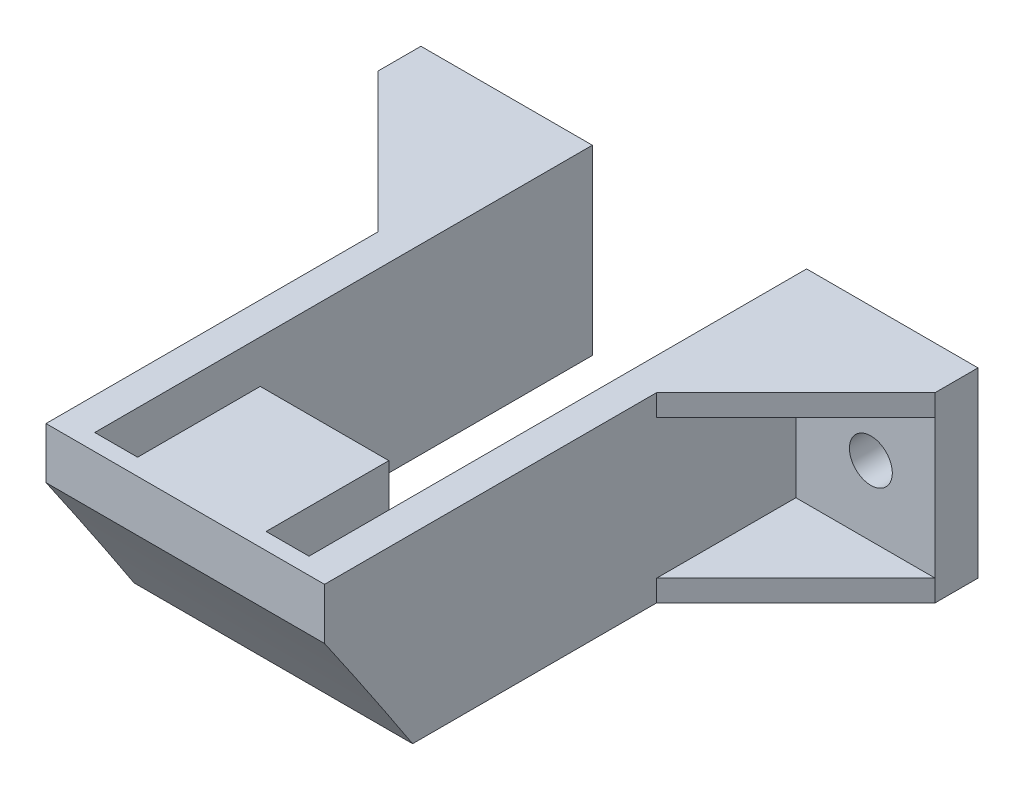
SolidWorks part; units mm, degrees
ref_plane "Front Plane" through (0, 0, 0) normal (0, 0, 1) x (1, 0, 0)
ref_plane "Top Plane" through (0, 0, 0) normal (0, 1, 0) x (1, 0, 0)
ref_plane "Right Plane" through (0, 0, 0) normal (1, 0, 0) x (0, 0, -1)
sketch "Sketch1" plane through (0, 0, 0) normal (0, 1, 0) x (1, 0, 0)
  line L0 (-7.9784, -3.6636) -> (12.0216, -3.6636)
  line L1 (-10.9784, -16.6636) -> (15.0216, -16.6636)
  line L2 (-7.9784, -3.6636) -> (-7.9784, 31.3364)
  line L3 (-10.9784, -16.6636) -> (-10.9784, 22.1528)
  line L4 (15.0216, -16.6636) -> (15.0216, 18.232)
  line L5 (12.0216, -3.6636) -> (12.0216, 31.3364)
  line L6 (-7.9784, 31.3364) -> (-23.9784, 31.3364)
  line L7 (-23.9784, 31.3364) -> (-23.9784, 27.3364)
  line L8 (-10.9784, 22.1528) -> (-10.9784, 27.3364)
  line L9 (-23.9784, 27.3364) -> (-10.9784, 27.3364)
  line L10 (12.0216, 31.3364) -> (28.0216, 31.3364)
  line L11 (28.0216, 31.3364) -> (28.0216, 27.3364)
  line L12 (28.0216, 27.3364) -> (15.0216, 27.3364)
  line L13 (15.0216, 27.3364) -> (15.0216, 18.232)
  dimension "D1" = 13
  dimension "D2" = 3
  dimension "D3" = 3
  dimension "D4" = 35
  dimension "D5" = 20
extrude "Boss-Extrude1" add sketch "Sketch1" along normal blind 17
sketch "Sketch4" plane through (0, 17, 0) normal (0, 1, 0) x (1, 0, 0)
  line L0 (-23.9784, 27.3364) -> (-10.9784, 14.3364)
  line L1 (-10.9784, 27.3364) -> (-10.9784, -16.6636) construction
  line L2 (-10.9784, 14.3364) -> (-10.9784, 27.3364)
  line L3 (-10.9784, 27.3364) -> (-23.9784, 27.3364)
  line L4 (28.0216, 27.3364) -> (15.0216, 14.3364)
  line L5 (15.0216, -16.6636) -> (15.0216, 27.3364) construction
  line L6 (15.0216, 14.3364) -> (15.0216, 27.3364)
  line L7 (15.0216, 27.3364) -> (28.0216, 27.3364)
extrude "Boss-Extrude2" add sketch "Sketch4" against normal blind 2
sketch "Sketch5" plane through (0, 0, 0) normal (0, -1, 0) x (1, 0, 0)
  line L0 (-23.9784, -27.3364) -> (-10.9784, -14.3364)
  line L1 (-10.9784, -14.3364) -> (-10.9784, -27.3364)
  line L2 (-10.9784, -27.3364) -> (-23.9784, -27.3364) construction
  line L3 (-10.9784, -14.3364) -> (-10.9784, -27.3364) construction
  line L4 (-10.9784, -27.3364) -> (-23.9784, -27.3364)
  line L5 (15.0216, -14.3364) -> (28.0216, -27.3364)
  line L6 (28.0216, -27.3364) -> (15.0216, -27.3364)
  line L7 (15.0216, -27.3364) -> (15.0216, -14.3364) construction
  line L8 (28.0216, -27.3364) -> (15.0216, -27.3364) construction
  line L9 (15.0216, -27.3364) -> (15.0216, -14.3364)
extrude "Boss-Extrude3" add sketch "Sketch5" against normal blind 2
sketch "Sketch6" plane through (0, 0, -31.3364) normal (0, 0, -1) x (-1, 0, 0)
  line L0 (-12.0216, 17) -> (-12.0216, 0) construction
  line L1 (7.9784, 17) -> (7.9784, 0) construction
  line L2 (10.9784, 2) -> (23.9784, 2) construction
  circle A0 centre (-22.0216, 8.5) radius 2
  circle A1 centre (17.9784, 8.5) radius 2
  dimension "D2" = 10
  dimension "D3" = 6.5
  dimension "D1" = 10
extrude "Cut-Extrude1" cut sketch "Sketch6" against normal blind 10
sketch "Sketch7" plane through (-7.9784, 0, 0) normal (1, 0, 0) x (0, 0, -1)
  line L0 (6.6603, 17) -> (-15.1139, 17)
  line L1 (-16.6636, 17) -> (14.3364, 17) construction
  line L2 (-3.6636, 0) -> (9.5993, 0)
  line L3 (-16.6636, 0) -> (14.3364, 0) construction
  line L4 (6.6603, 17) -> (9.5993, 0)
  arc A0 (65.0752, -145.6) -> (-100.4744, 114.6891) centre (-506.9613, -326.6365) ccw construction
  arc A1 (-3.6636, 0) -> (-15.1139, 17) centre (-506.9613, -326.6365) ccw
extrude "Cut-Extrude2" cut sketch "Sketch7" along normal blind 4
sketch "Sketch8" plane through (-10.9784, 0, 0) normal (-1, 0, 0) x (0, 0, 1)
  line L2 (21.6153, 19.2756) -> (46.6508, 12.9758)
  line L3 (46.6508, 12.9758) -> (28.9959, -26.912)
  line L4 (-0.6902, -14.3772) -> (28.9959, -26.912)
  arc A2 (21.6153, 19.2756) -> (-0.6902, -14.3772) centre (506.9613, -326.6365) ccw
extrude "Cut-Extrude3" cut sketch "Sketch8" against normal blind 100
sketch "Sketch9" plane through (12.0216, 0, 0) normal (-1, 0, 0) x (0, 0, 1)
  line L0 (-11.1882, 17) -> (-11.1882, 0)
  line L1 (-14.3364, 17) -> (16.6636, 17) construction
  line L2 (-14.3364, 0) -> (8.4389, 0) construction
  line L3 (-11.1882, 0) -> (3.6636, 0)
  line L4 (-11.1882, 17) -> (15.1139, 17)
  arc A0 (100.4744, 114.6891) -> (-65.0752, -145.6) centre (506.9613, -326.6365) ccw construction
  arc A1 (15.1139, 17) -> (3.6636, 0) centre (506.9613, -326.6365) ccw
extrude "Cut-Extrude4" cut sketch "Sketch9" along normal blind 4
